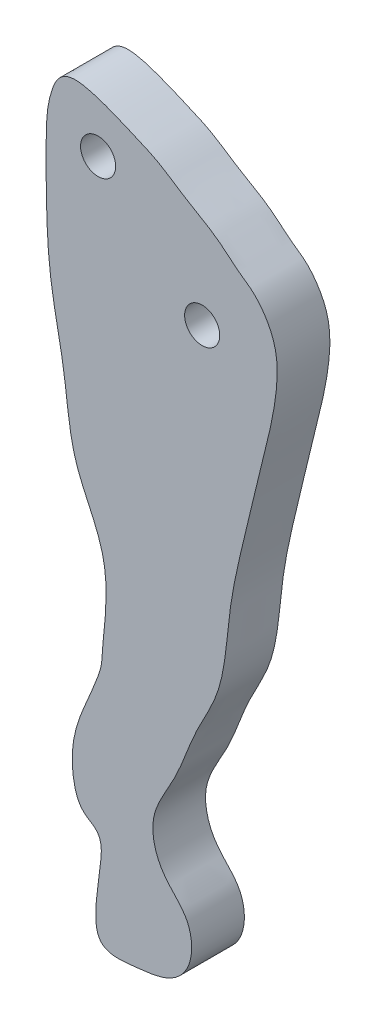
SolidWorks part; units mm, degrees
ref_plane "Спереди" through (0, 0, 0) normal (0, 0, 1) x (1, 0, 0)
ref_plane "Сверху" through (0, 0, 0) normal (0, 1, 0) x (1, 0, 0)
ref_plane "Справа" through (0, 0, 0) normal (1, 0, 0) x (0, 0, -1)
other "Configuration Table"
sketch "Sketch1" plane through (0, 0, 0) normal (0, 0, 1) x (1, 0, 0)
  circle A0 centre (-6.9471, 4.2899) radius 1
  circle A1 centre (-12.8747, 9.6623) radius 1
  spline S0 degree 3 poles (-15.8441, 9.5264) (-15.7245, 11.3822) (-14.6943, 13.3755) (-10.7472, 11.6856) (-9.3789, 11.1011) (-7.9356, 10.0667) (-6.0862, 9.0767) (-5.2241, 8.2406) (-4.4681, 7.6881) (-3.8196, 7.2649) (-2.6509, 5.6577) (-2.6299, 3.302) (-3.1021, 0.9077) (-3.6994, -1.3468) (-4.4707, -4.7299) (-5.5278, -8.8478) (-5.6314, -13.0445) (-7.5078, -16.094) (-8.3489, -18.8594) (-10.0992, -21.2773) (-9.4077, -23.9484) (-7.568, -25.2776) (-7.4213, -27.7007) (-8.6939, -29.0444) (-11.0194, -29.2758) (-13.2741, -29.5418) (-12.747, -24.9861) (-12.4487, -23.6774) (-14.1267, -22.9906) (-14.5673, -19.9678) (-12.4673, -15.1429) (-12.8446, -15.7321) (-12.0345, -9.8014) (-14.4535, -6.3482) (-14.6831, -1.986) (-15.7086, 2.2192) (-15.8378, 5.9902) (-15.8441, 9.5264) (-15.7245, 11.3822) (-14.6943, 13.3755) knots -0.107085 -0.057315 -0.028029 0 0.019168 0.035852 0.049221 0.065363 0.080616 0.094734 0.09682 0.101479 0.125428 0.150735 0.177783 0.196742 0.232864 0.285139 0.334734 0.362744 0.397642 0.427729 0.452921 0.476299 0.496976 0.520565 0.535628 0.556474 0.575337 0.609705 0.622666 0.634741 0.653971 0.715132 0.757144 0.80452 0.849469 0.892915 0.942685 0.971971 1 1.019168 1.035852 1.049221 only from (-15.4682, 11.7127) to (-15.4682, 11.7127)
  dimension "D2" = 2
  dimension "D1" = 8
extrude "Boss-Extrude1" add sketch "Sketch1" along normal blind 3
equation "\"R small\"= 2"
equation "\"R big\"= 4"
equation "\"width\"= 0.6"
equation "\"border width\"= 1"
equation "\"D2@Sketch1\"=\"R small\""
